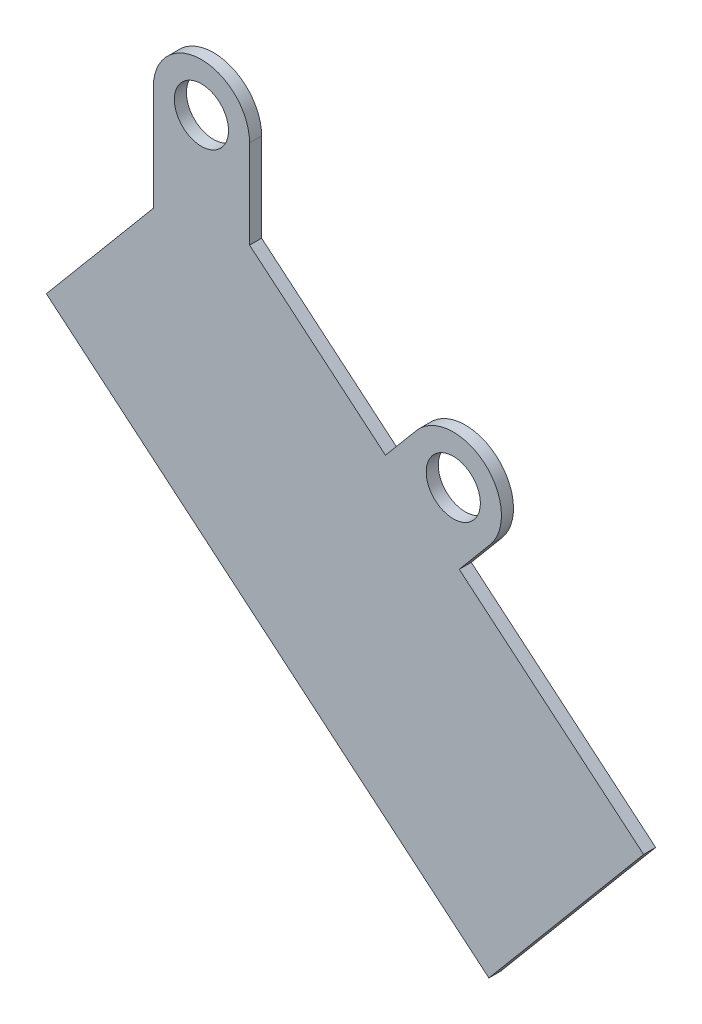
SolidWorks part; units mm, degrees
ref_plane "Front Plane" through (0, 0, 0) normal (0, 0, 1) x (1, 0, 0)
ref_plane "Top Plane" through (0, 0, 0) normal (0, 1, 0) x (1, 0, 0)
ref_plane "Right Plane" through (0, 0, 0) normal (1, 0, 0) x (0, 0, -1)
sketch "Sketch1" plane through (0, 0, 0) normal (0, 0, 1) x (1, 0, 0)
  line L0 (-56.4212, 233.0694) -> (177.0692, 37.1477)
  line L1 (177.0692, 37.1477) -> (258.7032, 134.4354)
  line L2 (258.7032, 134.4354) -> (161.4155, 216.0694)
  line L3 (0, 300.3095) -> (-56.4212, 233.0694)
  line L4 (50.8, 355.6) -> (50.8, 308.8869)
  line L5 (0, 381) -> (50.8, 381) construction
  line L6 (0, 381) -> (0, 0) construction
  line L7 (0, 0) -> (50.8, 0) construction
  line L8 (50.8, 381) -> (50.8, 0) construction
  line L9 (-101.6, 0) -> (-152.4, 0) construction
  line L10 (-101.6, 0) -> (-101.6, 762) construction
  line L11 (-101.6, 762) -> (-152.4, 762) construction
  line L12 (-152.4, 0) -> (-152.4, 762) construction
  line L13 (0, 355.6) -> (0, 300.3095)
  line L14 (60.324, 135.1086) -> (158.2848, 251.8537) construction
  line L15 (138.8273, 268.1805) -> (122.5005, 248.723)
  line L16 (177.7424, 235.5269) -> (161.4155, 216.0694)
  line L17 (177.7424, 235.5269) -> (138.8273, 268.1805) construction
  line L18 (122.5005, 248.723) -> (50.8, 308.8869)
  circle A0 centre (25.4, 355.6) radius 14.2875
  circle A1 centre (25.4, 355.6) radius 12.7
  arc A2 (0, 355.6) -> (50.8, 355.6) centre (25.4, 355.6) cw
  circle A3 centre (158.2848, 251.8537) radius 14.2875
  arc A4 (138.8273, 268.1805) -> (177.7424, 235.5269) centre (158.2848, 251.8537) cw
  point P7 (25.4, 381)
  point P19 (135.7846, 263.6393)
  dimension "D1" = 28.575
  dimension "D11" = 25.4
  dimension "D7" = 25.4
  dimension "D15" = 28.575
  dimension "D17" = 25.4
  dimension "D2" = 127
  dimension "D3" = 304.8
  dimension "D4" = 50.8
  dimension "D5" = 25.4
  dimension "D6" = 381
  dimension "D8" = 50.8
  dimension "D9" = 762
  dimension "D10" = 101.6
  dimension "D12" = 87.7758
  dimension "D13" = 55.2905
  dimension "D14" = 40
  dimension "D16" = 25.4
extrude "Boss-Extrude1" add sketch "Sketch1" along normal mid plane 6.35 contours A2 L13 L3 L0 L1 L2 L4 A0
